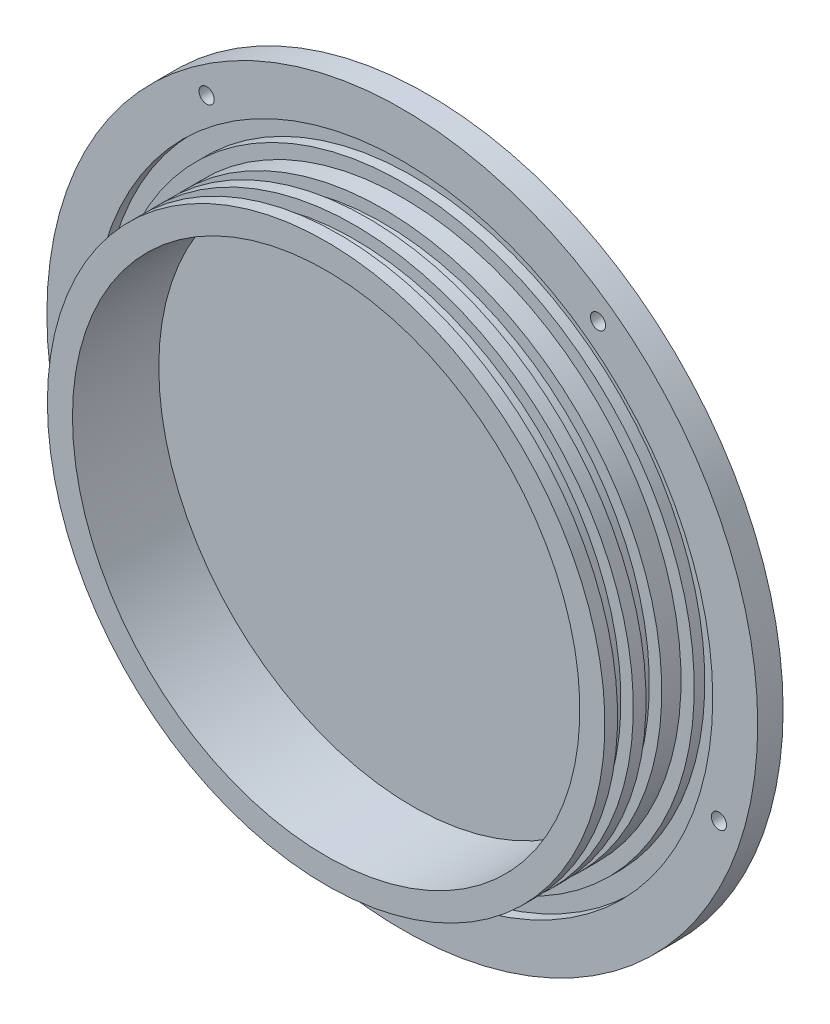
SolidWorks part; units mm, degrees
ref_plane "Front Plane" through (0, 0, 0) normal (0, 0, 1) x (1, 0, 0)
ref_plane "Top Plane" through (0, 0, 0) normal (0, 1, 0) x (1, 0, 0)
ref_plane "Right Plane" through (0, 0, 0) normal (1, 0, 0) x (0, 0, -1)
sketch "Sketch1" plane through (0, 0, 0) normal (0, 1, 0) x (1, 0, 0)
  line L0 (0, 0) -> (0, -25.4) construction
  line L1 (0, 0) -> (88.9, 0)
  line L2 (63.4492, -25.4) -> (69.723, -25.4)
  line L3 (69.723, -25.4) -> (69.723, -22.225)
  line L4 (63.4492, -25.4) -> (63.4492, -3.8118)
  line L5 (63.4492, -3.8118) -> (0, -3.8118)
  line L6 (0, -3.8118) -> (0, 0)
  line L7 (88.9, 0) -> (88.9, -6.35)
  line L8 (73.025, -3.7084) -> (77.6478, -3.7084)
  line L9 (73.025, -3.7084) -> (73.025, -6.35)
  line L10 (73.025, -6.35) -> (69.723, -6.35)
  line L11 (77.6478, -3.7084) -> (77.6478, -6.35)
  line L12 (77.6478, -6.35) -> (88.9, -6.35)
  line L13 (69.723, -22.225) -> (66.6242, -22.225)
  line L14 (66.6242, -22.225) -> (66.6242, -18.288)
  line L15 (66.6242, -18.288) -> (69.723, -18.288)
  line L16 (69.723, -15.113) -> (66.6242, -15.113)
  line L17 (66.6242, -15.113) -> (66.6242, -11.176)
  line L18 (66.6242, -11.176) -> (69.723, -11.176)
  line L19 (69.723, -11.176) -> (69.723, -6.35)
  line L20 (69.723, -18.288) -> (69.723, -15.113)
  dimension "D1" = 139.446
  dimension "D2" = 6.35
  dimension "D3" = 177.8
  dimension "D4" = 146.05
  dimension "D5" = 3.175
  dimension "D6" = 19.05
  dimension "D7" = 4.6228
  dimension "D8" = 2.6416
  dimension "D9" = 3.0988
  dimension "D10" = 3.937
  dimension "D11" = 3.175
  dimension "D12" = 3.175
revolve "Revolve1" add sketch "Sketch1" angle 360 about L0
hole_wizard "#6 Clearance Hole1" positions "Sketch3" profile "Sketch2" hole size "#6" standard "ANSI Inch"
sketch "Sketch3" plane through (0, 0, 6.35) normal (0, 0, 1) x (1, 0, 0)
  line L0 (0, 77.6478) -> (0, 83.2739) construction
  line L3 (0, 83.2739) -> (0, 88.9) construction
  line L5 (0, 0) -> (0, -83.2739) construction
  line L8 (0, 0) -> (79.1982, -25.7331) construction
  line L11 (0, 0) -> (48.9472, 67.37) construction
  circle A1 centre (0, 0) radius 83.2739
  circle A2 centre (0, 0) radius 77.6478 construction
  circle A3 centre (0, 0) radius 77.6478 construction
  circle A4 centre (0, 0) radius 88.9 construction
  point P26 (0, -83.2739)
  point P32 (79.1982, -25.7331)
  point P38 (48.9472, 67.37)
  point P51 (-79.1982, -25.7331)
  point P52 (-48.9472, 67.37)
  dimension "D1" = 72
  dimension "D2" = 72
sketch "Sketch2" plane through (0, -83.2739, 6.35) normal (1, 0, 0) x (0, -1, 0)
  line L0 (0, 0) -> (0, 26.5408)
  line L1 (0, 26.5408) -> (1.8986, 25.4)
  line L2 (1.8986, 25.4) -> (1.8986, 0)
  line L5 (1.8986, 0) -> (0, 0)
  line L10 (0, 26.5408) -> (-1.8986, 25.4) construction
  line L11 (0, -6.35) -> (0, 107.95) construction
  dimension "Hole Dia." = 3.7973
  dimension "Hole Depth" = 25.4
  dimension "Drill Angle" = 118
